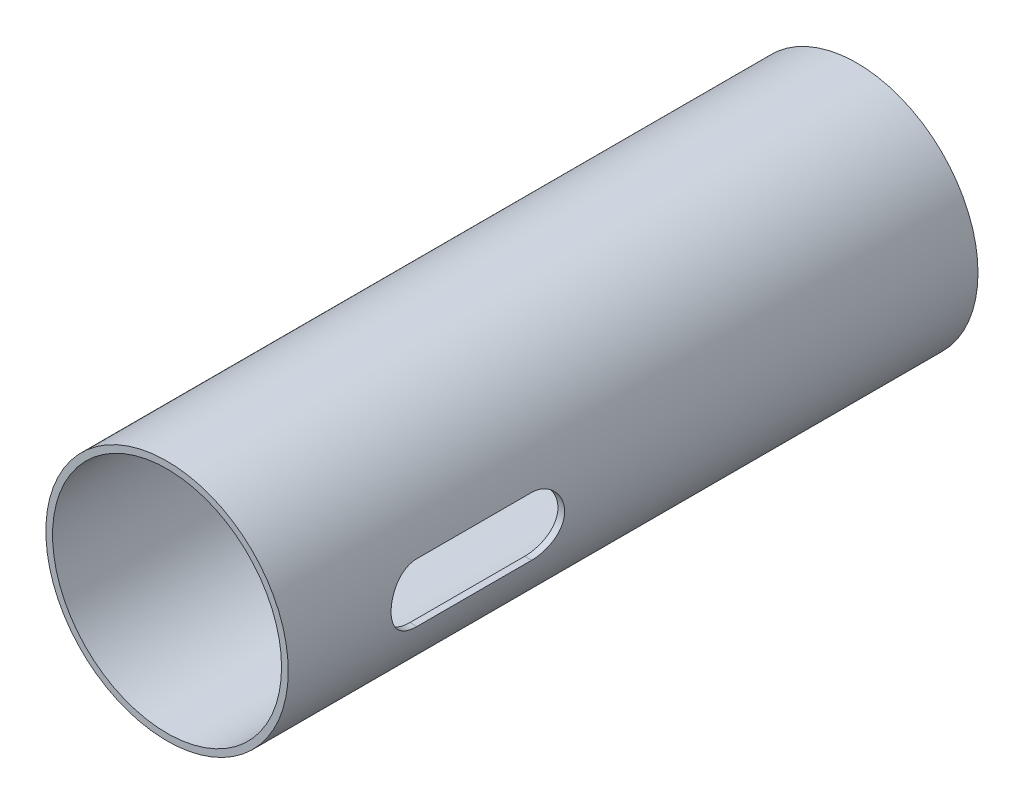
SolidWorks part; units mm, degrees
material "3003 Alloy"
ref_plane "Front Plane" through (0, 0, 0) normal (0, 0, 1) x (1, 0, 0)
ref_plane "Top Plane" through (0, 0, 0) normal (0, 1, 0) x (1, 0, 0)
ref_plane "Right Plane" through (0, 0, 0) normal (1, 0, 0) x (0, 0, -1)
sketch "Sketch1" plane through (0, 0, 0) normal (0, 0, 1) x (1, 0, 0)
  circle A0 centre (-89.675, 9.5336) radius 12.6309
extrude "Boss-Extrude1" add sketch "Sketch1" along normal blind 71.882
shell "Shell1" thickness 0.6985
ref_plane "Plane1" through (-89.662, 0, 0) normal (1, 0, 0) x (0, 0, -1)
sketch "Sketch4" plane through (-89.662, 0, 0) normal (1, 0, 0) x (0, 0, -1)
  line L3 (-58.1025, 12.5943) -> (-46.1391, 12.5943)
  line L4 (-58.1025, 6.4729) -> (-46.1391, 6.4729)
  arc A0 (-58.1025, 12.5943) -> (-58.1025, 6.4729) centre (-58.1025, 9.5336) ccw
  arc A1 (-46.1391, 6.4729) -> (-46.1391, 12.5943) centre (-46.1391, 9.5336) ccw
extrude "Cut-Extrude1" cut sketch "Sketch4" along normal blind 71.882
